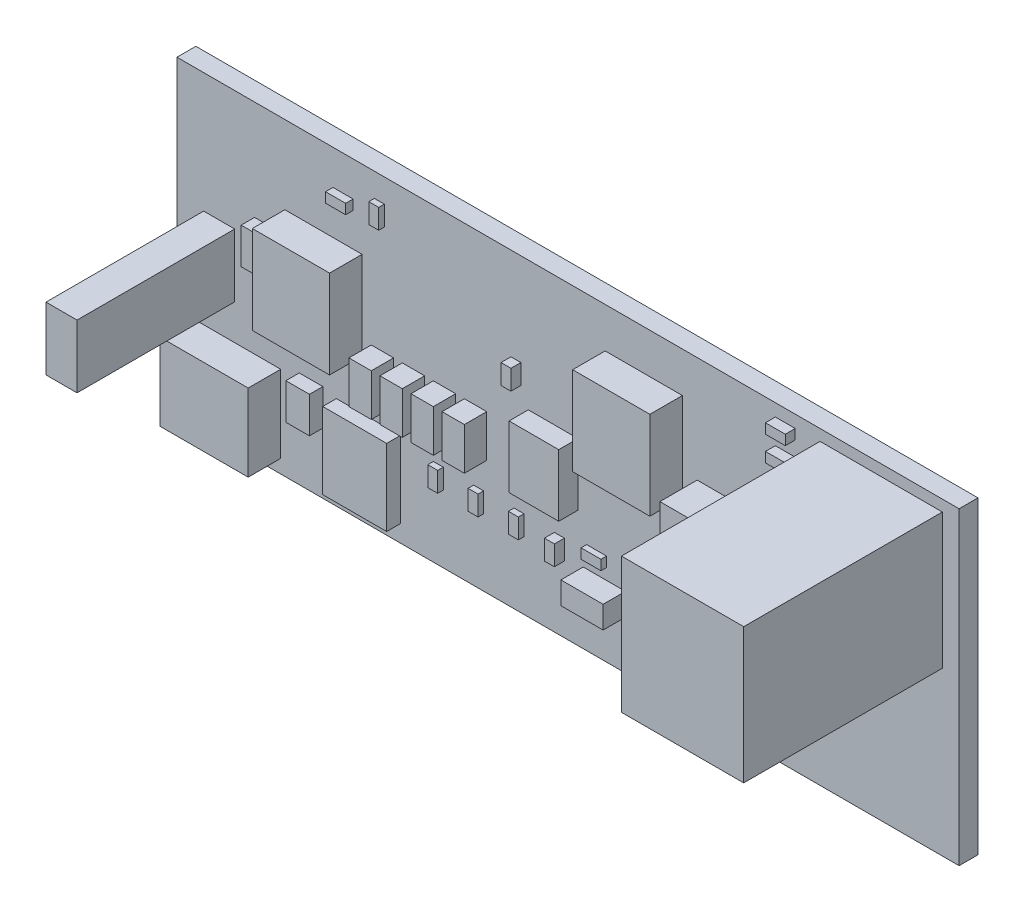
SolidWorks part; units mm, degrees
ref_plane "Спереди" through (0, 0, 0) normal (0, 0, 1) x (1, 0, 0)
ref_plane "Сверху" through (0, 0, 0) normal (0, 1, 0) x (1, 0, 0)
ref_plane "Справа" through (0, 0, 0) normal (1, 0, 0) x (0, 0, -1)
sketch "Эскиз1" plane through (0, 0, 0) normal (0, 0, 1) x (1, 0, 0)
  line L0 (0, 0) -> (0, 24.9)
  line L1 (0, 24.9) -> (63, 24.9)
  line L2 (63, 24.9) -> (63, 0)
  line L3 (63, 0) -> (0, 0)
extrude "BOARD" add sketch "Эскиз1" along normal blind 1.522 separate body
ref_plane "Плоскость4" through (0, 0, 1.522) normal (0, 0, 1) x (1, 0, 0)
sketch "Эскиз2" plane through (0, 0, 1.522) normal (0, 0, 1) x (1, 0, 0)
  line L0 (4.6502, 10.1598) -> (2.1502, 10.1598)
  line L1 (2.1502, 10.1598) -> (2.1502, 15.2398)
  line L2 (2.1502, 15.2398) -> (4.6502, 15.2398)
  line L3 (4.6502, 15.2398) -> (4.6502, 10.1598)
extrude "TE_826629-2-1" add sketch "Эскиз2" along normal blind 12.7 separate body
sketch "Эскиз3" plane through (0, 0, 1.522) normal (0, 0, 1) x (1, 0, 0)
  line L0 (19.95, 11.85) -> (19.95, 10.05)
  line L1 (19.95, 10.05) -> (19.95, 9.25)
  line L2 (19.95, 9.25) -> (18.15, 9.25)
  line L3 (18.15, 9.25) -> (18.15, 10.05)
  line L4 (18.15, 10.05) -> (18.15, 11.85)
  line L5 (18.15, 11.85) -> (18.15, 12.65)
  line L6 (18.15, 12.65) -> (19.95, 12.65)
  line L7 (19.95, 12.65) -> (19.95, 11.85)
extrude "C1206-1" add sketch "Эскиз3" along normal blind 1.8 separate body
sketch "Эскиз4" plane through (0, 0, 1.522) normal (0, 0, 1) x (1, 0, 0)
  line L0 (8.15, 13.95) -> (6.25, 13.95)
  line L1 (6.25, 13.95) -> (6.25, 16.85)
  line L2 (6.25, 16.85) -> (8.15, 16.85)
  line L3 (8.15, 16.85) -> (8.15, 13.95)
extrude "DO-219AB-1" add sketch "Эскиз4" along normal blind 1.08 separate body
sketch "Эскиз5" plane through (0, 0, 1.522) normal (0, 0, 1) x (1, 0, 0)
  line L0 (35.325, 3.9) -> (33.525, 3.9)
  line L1 (33.525, 3.9) -> (32.725, 3.9)
  line L2 (32.725, 3.9) -> (32.725, 5.7)
  line L3 (32.725, 5.7) -> (33.525, 5.7)
  line L4 (33.525, 5.7) -> (35.325, 5.7)
  line L5 (35.325, 5.7) -> (36.125, 5.7)
  line L6 (36.125, 5.7) -> (36.125, 3.9)
  line L7 (36.125, 3.9) -> (35.325, 3.9)
extrude "C1206-2" add sketch "Эскиз5" along normal blind 1.8 separate body
sketch "Эскиз6" plane through (0, 0, 1.522) normal (0, 0, 1) x (1, 0, 0)
  line L0 (31.2002, 5.3498) -> (30.4002, 5.3498)
  line L1 (30.4002, 5.3498) -> (30.4002, 6.9499)
  line L2 (30.4002, 6.9499) -> (31.2002, 6.9499)
  line L3 (31.2002, 6.9499) -> (31.2002, 5.3498)
extrude "C0603-1" add sketch "Эскиз6" along normal blind 0.8 separate body
sketch "Эскиз7" plane through (0, 0, 1.522) normal (0, 0, 1) x (1, 0, 0)
  line L0 (61.6501, 13.1001) -> (51.8001, 13.1001)
  line L1 (51.8001, 13.1001) -> (51.8001, 24.0001)
  line L2 (51.8001, 24.0001) -> (61.6501, 24.0001)
  line L3 (61.6501, 24.0001) -> (61.6501, 13.1001)
extrude "4-1775099-0-1" add sketch "Эскиз7" along normal blind 16 separate body
sketch "Эскиз8" plane through (0, 0, 1.522) normal (0, 0, 1) x (1, 0, 0)
  line L0 (17.99, 1.355) -> (12.84, 1.355)
  line L1 (12.84, 1.355) -> (12.84, 7.505)
  line L2 (12.84, 7.505) -> (17.99, 7.505)
  line L3 (17.99, 7.505) -> (17.99, 1.355)
extrude "SON-8-1" add sketch "Эскиз8" along normal blind 1.1 separate body
sketch "Эскиз9" plane through (0, 0, 1.522) normal (0, 0, 1) x (1, 0, 0)
  line L0 (40.71, 14.545) -> (34.49, 14.545)
  line L1 (34.49, 14.545) -> (34.49, 21.655)
  line L2 (34.49, 21.655) -> (40.71, 21.655)
  line L3 (40.71, 21.655) -> (40.71, 14.545)
extrude "DO-214AB-1" add sketch "Эскиз9" along normal blind 2.62 separate body
sketch "Эскиз10" plane through (0, 0, 1.522) normal (0, 0, 1) x (1, 0, 0)
  line L0 (1.245, 1.09) -> (1.245, 7.31)
  line L1 (1.245, 7.31) -> (8.355, 7.31)
  line L2 (8.355, 7.31) -> (8.355, 1.09)
  line L3 (8.355, 1.09) -> (1.245, 1.09)
extrude "DO-214AB-2" add sketch "Эскиз10" along normal blind 2.62 separate body
sketch "Эскиз11" plane through (0, 0, 1.522) normal (0, 0, 1) x (1, 0, 0)
  line L0 (9.85, 7.8) -> (11.75, 7.8)
  line L1 (11.75, 7.8) -> (11.75, 4.9)
  line L2 (11.75, 4.9) -> (9.85, 4.9)
  line L3 (9.85, 4.9) -> (9.85, 7.8)
extrude "DO-219AB-2" add sketch "Эскиз11" along normal blind 1.08 separate body
sketch "Эскиз12" plane through (0, 0, 1.522) normal (0, 0, 1) x (1, 0, 0)
  line L0 (14.91, 11.495) -> (8.69, 11.495)
  line L1 (8.69, 11.495) -> (8.69, 18.605)
  line L2 (8.69, 18.605) -> (14.91, 18.605)
  line L3 (14.91, 18.605) -> (14.91, 11.495)
extrude "DO-214AB-3" add sketch "Эскиз12" along normal blind 2.62 separate body
sketch "Эскиз13" plane through (0, 0, 1.522) normal (0, 0, 1) x (1, 0, 0)
  line L0 (51.0999, 4.6001) -> (49.4999, 4.6001)
  line L1 (49.4999, 4.6001) -> (49.4999, 5.4001)
  line L2 (49.4999, 5.4001) -> (51.0999, 5.4001)
  line L3 (51.0999, 5.4001) -> (51.0999, 4.6001)
extrude "R0603-1" add sketch "Эскиз13" along normal blind 0.45 separate body
sketch "Эскиз14" plane through (0, 0, 1.522) normal (0, 0, 1) x (1, 0, 0)
  line L0 (43.7499, 5.0501) -> (42.1499, 5.0501)
  line L1 (42.1499, 5.0501) -> (42.1499, 5.8501)
  line L2 (42.1499, 5.8501) -> (43.7499, 5.8501)
  line L3 (43.7499, 5.8501) -> (43.7499, 5.0501)
extrude "R0603-2" add sketch "Эскиз14" along normal blind 0.45 separate body
sketch "Эскиз15" plane through (0, 0, 1.522) normal (0, 0, 1) x (1, 0, 0)
  line L0 (42.1751, 3.8499) -> (43.7751, 3.8499)
  line L1 (43.7751, 3.8499) -> (43.7751, 3.0499)
  line L2 (43.7751, 3.0499) -> (42.1751, 3.0499)
  line L3 (42.1751, 3.0499) -> (42.1751, 3.8499)
extrude "R0603-3" add sketch "Эскиз15" along normal blind 0.45 separate body
sketch "Эскиз16" plane through (0, 0, 1.522) normal (0, 0, 1) x (1, 0, 0)
  line L0 (34.5999, 6.6001) -> (32.9999, 6.6001)
  line L1 (32.9999, 6.6001) -> (32.9999, 7.4001)
  line L2 (32.9999, 7.4001) -> (34.5999, 7.4001)
  line L3 (34.5999, 7.4001) -> (34.5999, 6.6001)
extrude "R0603-4" add sketch "Эскиз16" along normal blind 0.45 separate body
sketch "Эскиз17" plane through (0, 0, 1.522) normal (0, 0, 1) x (1, 0, 0)
  line L0 (27.1501, 5.4251) -> (27.1501, 7.0251)
  line L1 (27.1501, 7.0251) -> (27.9501, 7.0251)
  line L2 (27.9501, 7.0251) -> (27.9501, 5.4251)
  line L3 (27.9501, 5.4251) -> (27.1501, 5.4251)
extrude "R0603-5" add sketch "Эскиз17" along normal blind 0.45 separate body
sketch "Эскиз18" plane through (0, 0, 1.522) normal (0, 0, 1) x (1, 0, 0)
  line L0 (21.4499, 7.0249) -> (21.4499, 5.4249)
  line L1 (21.4499, 5.4249) -> (20.6499, 5.4249)
  line L2 (20.6499, 5.4249) -> (20.6499, 7.0249)
  line L3 (20.6499, 7.0249) -> (21.4499, 7.0249)
extrude "R0603-6" add sketch "Эскиз18" along normal blind 0.45 separate body
sketch "Эскиз19" plane through (0, 0, 1.522) normal (0, 0, 1) x (1, 0, 0)
  line L0 (23.9001, 5.4001) -> (23.9001, 7.0001)
  line L1 (23.9001, 7.0001) -> (24.7001, 7.0001)
  line L2 (24.7001, 7.0001) -> (24.7001, 5.4001)
  line L3 (24.7001, 5.4001) -> (23.9001, 5.4001)
extrude "R0603-7" add sketch "Эскиз19" along normal blind 0.45 separate body
sketch "Эскиз20" plane through (0, 0, 1.522) normal (0, 0, 1) x (1, 0, 0)
  line L0 (6.9001, 10.4001) -> (6.9001, 12.0001)
  line L1 (6.9001, 12.0001) -> (7.7001, 12.0001)
  line L2 (7.7001, 12.0001) -> (7.7001, 10.4001)
  line L3 (7.7001, 10.4001) -> (6.9001, 10.4001)
extrude "R0603-8" add sketch "Эскиз20" along normal blind 0.45 separate body
sketch "Эскиз21" plane through (0, 0, 1.522) normal (0, 0, 1) x (1, 0, 0)
  line L0 (16.6999, 22.9999) -> (16.6999, 21.3999)
  line L1 (16.6999, 21.3999) -> (15.8999, 21.3999)
  line L2 (15.8999, 21.3999) -> (15.8999, 22.9999)
  line L3 (15.8999, 22.9999) -> (16.6999, 22.9999)
extrude "R0603-9" add sketch "Эскиз21" along normal blind 0.45 separate body
sketch "Эскиз22" plane through (0, 0, 1.522) normal (0, 0, 1) x (1, 0, 0)
  line L0 (49.5, 9.45) -> (41.9, 9.45)
  line L1 (41.9, 9.45) -> (41.9, 16.35)
  line L2 (41.9, 16.35) -> (49.5, 16.35)
  line L3 (49.5, 16.35) -> (49.5, 9.45)
extrude "SRP-2-670X660X280-1" add sketch "Эскиз22" along normal blind 3 separate body
sketch "Эскиз23" plane through (0, 0, 1.522) normal (0, 0, 1) x (1, 0, 0)
  line L0 (51.0851, 2.7749) -> (49.465, 2.7749)
  line L1 (49.465, 2.7749) -> (49.465, 3.5749)
  line L2 (49.465, 3.5749) -> (51.0851, 3.5749)
  line L3 (51.0851, 3.5749) -> (51.0851, 2.7749)
extrude "HL0603-1" add sketch "Эскиз23" along normal blind 0.6 separate body
sketch "Эскиз24" plane through (0, 0, 1.522) normal (0, 0, 1) x (1, 0, 0)
  line L0 (14.1851, 21.2999) -> (12.565, 21.2999)
  line L1 (12.565, 21.2999) -> (12.565, 22.0999)
  line L2 (12.565, 22.0999) -> (14.1851, 22.0999)
  line L3 (14.1851, 22.0999) -> (14.1851, 21.2999)
extrude "HL0603-2" add sketch "Эскиз24" along normal blind 0.6 separate body
sketch "Эскиз25" plane through (0, 0, 1.522) normal (0, 0, 1) x (1, 0, 0)
  line L0 (32.3, 9.45) -> (28.3, 9.45)
  line L1 (28.3, 9.45) -> (28.3, 14.45)
  line L2 (28.3, 14.45) -> (32.3, 14.45)
  line L3 (32.3, 14.45) -> (32.3, 9.45)
extrude "HSOIC-8-1" add sketch "Эскиз25" along normal blind 1.55 separate body
sketch "Эскиз26" plane through (0, 0, 1.522) normal (0, 0, 1) x (1, 0, 0)
  line L0 (48.1998, 23.0998) -> (48.1998, 23.8998)
  line L1 (48.1998, 23.8998) -> (49.7999, 23.8998)
  line L2 (49.7999, 23.8998) -> (49.7999, 23.0998)
  line L3 (49.7999, 23.0998) -> (48.1998, 23.0998)
extrude "C0603-2" add sketch "Эскиз26" along normal blind 0.8 separate body
sketch "Эскиз27" plane through (0, 0, 1.522) normal (0, 0, 1) x (1, 0, 0)
  line L0 (48.1998, 21.0998) -> (48.1998, 21.8998)
  line L1 (48.1998, 21.8998) -> (49.7999, 21.8998)
  line L2 (49.7999, 21.8998) -> (49.7999, 21.0998)
  line L3 (49.7999, 21.0998) -> (48.1998, 21.0998)
extrude "C0603-3" add sketch "Эскиз27" along normal blind 0.8 separate body
sketch "Эскиз28" plane through (0, 0, 1.522) normal (0, 0, 1) x (1, 0, 0)
  line L0 (48.1498, 19.0998) -> (48.1498, 19.8998)
  line L1 (48.1498, 19.8998) -> (49.7499, 19.8998)
  line L2 (49.7499, 19.8998) -> (49.7499, 19.0998)
  line L3 (49.7499, 19.0998) -> (48.1498, 19.0998)
extrude "C0603-4" add sketch "Эскиз28" along normal blind 0.8 separate body
sketch "Эскиз29" plane through (0, 0, 1.522) normal (0, 0, 1) x (1, 0, 0)
  line L0 (48.1998, 17.0998) -> (48.1998, 17.8998)
  line L1 (48.1998, 17.8998) -> (49.7999, 17.8998)
  line L2 (49.7999, 17.8998) -> (49.7999, 17.0998)
  line L3 (49.7999, 17.0998) -> (48.1998, 17.0998)
extrude "C0603-5" add sketch "Эскиз29" along normal blind 0.8 separate body
sketch "Эскиз30" plane through (0, 0, 1.522) normal (0, 0, 1) x (1, 0, 0)
  line L0 (26.8998, 17.4502) -> (27.6998, 17.4502)
  line L1 (27.6998, 17.4502) -> (27.6998, 15.8501)
  line L2 (27.6998, 15.8501) -> (26.8998, 15.8501)
  line L3 (26.8998, 15.8501) -> (26.8998, 17.4502)
extrude "C0603-6" add sketch "Эскиз30" along normal blind 0.8 separate body
sketch "Эскиз31" plane through (0, 0, 1.522) normal (0, 0, 1) x (1, 0, 0)
  line L0 (24.95, 11.85) -> (24.95, 10.05)
  line L1 (24.95, 10.05) -> (24.95, 9.25)
  line L2 (24.95, 9.25) -> (23.15, 9.25)
  line L3 (23.15, 9.25) -> (23.15, 10.05)
  line L4 (23.15, 10.05) -> (23.15, 11.85)
  line L5 (23.15, 11.85) -> (23.15, 12.65)
  line L6 (23.15, 12.65) -> (24.95, 12.65)
  line L7 (24.95, 12.65) -> (24.95, 11.85)
extrude "C1206-3" add sketch "Эскиз31" along normal blind 1.8 separate body
sketch "Эскиз32" plane through (0, 0, 1.522) normal (0, 0, 1) x (1, 0, 0)
  line L0 (22.45, 11.85) -> (22.45, 10.05)
  line L1 (22.45, 10.05) -> (22.45, 9.25)
  line L2 (22.45, 9.25) -> (20.65, 9.25)
  line L3 (20.65, 9.25) -> (20.65, 10.05)
  line L4 (20.65, 10.05) -> (20.65, 11.85)
  line L5 (20.65, 11.85) -> (20.65, 12.65)
  line L6 (20.65, 12.65) -> (22.45, 12.65)
  line L7 (22.45, 12.65) -> (22.45, 11.85)
extrude "C1206-4" add sketch "Эскиз32" along normal blind 1.8 separate body
sketch "Эскиз33" plane through (0, 0, 1.522) normal (0, 0, 1) x (1, 0, 0)
  line L0 (17.45, 11.85) -> (17.45, 10.05)
  line L1 (17.45, 10.05) -> (17.45, 9.25)
  line L2 (17.45, 9.25) -> (15.65, 9.25)
  line L3 (15.65, 9.25) -> (15.65, 10.05)
  line L4 (15.65, 10.05) -> (15.65, 11.85)
  line L5 (15.65, 11.85) -> (15.65, 12.65)
  line L6 (15.65, 12.65) -> (17.45, 12.65)
  line L7 (17.45, 12.65) -> (17.45, 11.85)
extrude "C1206-5" add sketch "Эскиз33" along normal blind 1.8 separate body
